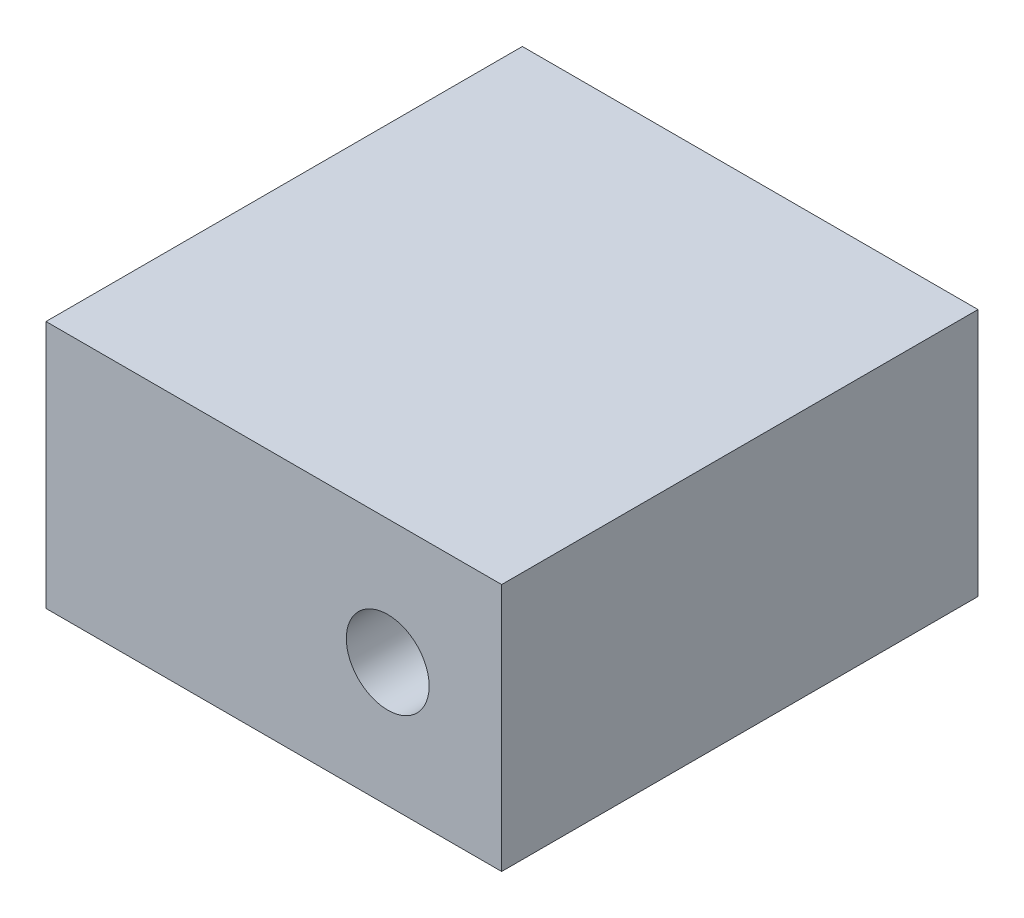
SolidWorks part; units mm, degrees
ref_plane "Front Plane" through (0, 0, 0) normal (0, 0, 1) x (1, 0, 0)
ref_plane "Top Plane" through (0, 0, 0) normal (0, 1, 0) x (1, 0, 0)
ref_plane "Right Plane" through (0, 0, 0) normal (1, 0, 0) x (0, 0, -1)
sketch "Sketch1" plane through (0, 0, 0) normal (0, 0, 1) x (1, 0, 0)
  line L1 (0, 0) -> (22, 0)
  line L2 (0, 0) -> (0, 12)
  line L3 (0, 12) -> (22, 12)
  line L4 (22, 0) -> (22, 12)
  dimension "D1" = 22
  dimension "D2" = 12
extrude "Boss-Extrude1" add sketch "Sketch1" along normal blind 23
sketch "Sketch2" plane through (0, 0, 23) normal (0, 0, 1) x (1, 0, 0)
  circle A0 centre (16.5, 6) radius 2
  dimension "D1" = 4
extrude "Cut-Extrude1" cut sketch "Sketch2" against normal blind 11
